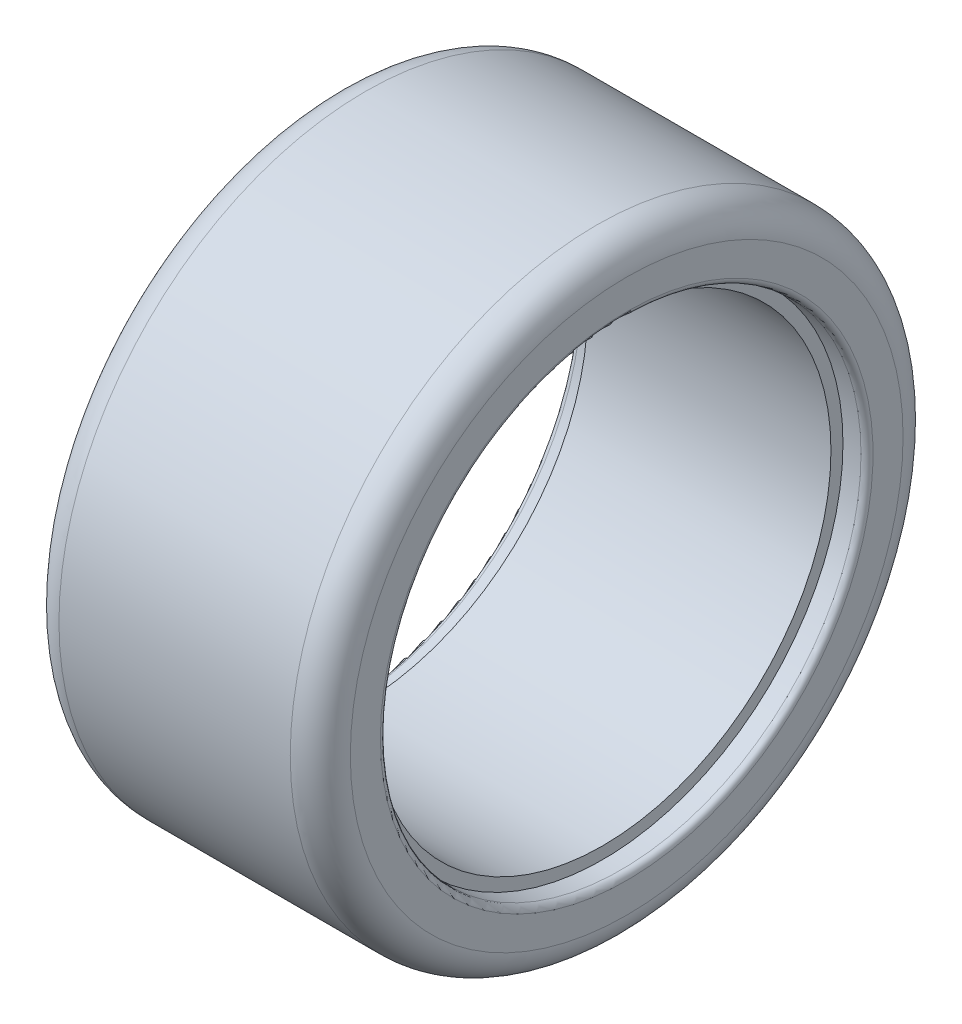
SolidWorks part; units mm, degrees
material "Delrin 2700 NC010, Low Viscosity Acetal Copolymer (SS)"
ref_plane "Front Plane" through (0, 0, 0) normal (0, 0, 1) x (1, 0, 0)
ref_plane "Top Plane" through (0, 0, 0) normal (0, 1, 0) x (1, 0, 0)
ref_plane "Right Plane" through (0, 0, 0) normal (1, 0, 0) x (0, 0, -1)
sketch "Sketch1" plane through (0, 0, 0) normal (0, 1, 0) x (1, 0, 0)
  line L0 (0, 19) -> (10.125, 19)
  line L1 (10.125, 19) -> (10.125, 20)
  line L2 (10.125, 20) -> (12.125, 20)
  line L3 (12.125, 20) -> (12.125, 25.5)
  line L4 (12.125, 25.5) -> (0, 25.5)
  line L5 (0, 25.5) -> (0, 19)
  line L6 (0, 0) -> (12.125, 0) construction
  dimension "D1" = 25.5
  dimension "D2" = 12.125
  dimension "D3" = 2
  dimension "D4" = 1
  dimension "D5" = 20
revolve "Revolve1" add sketch "Sketch1" angle 360 about L6
mirror "Mirror1" about plane through (0, 0, 0) normal (1, 0, 0) of "Revolve1"
fillet "Fillet1" radius 2.5 2 edges at (-12.125, 0, 25.5) (12.125, 0, 25.5)
fillet "Fillet2" radius 0.5 2 edges at (12.125, 0, 20) (-12.125, 0, 20)
equation "\"e\"=4.82414"
